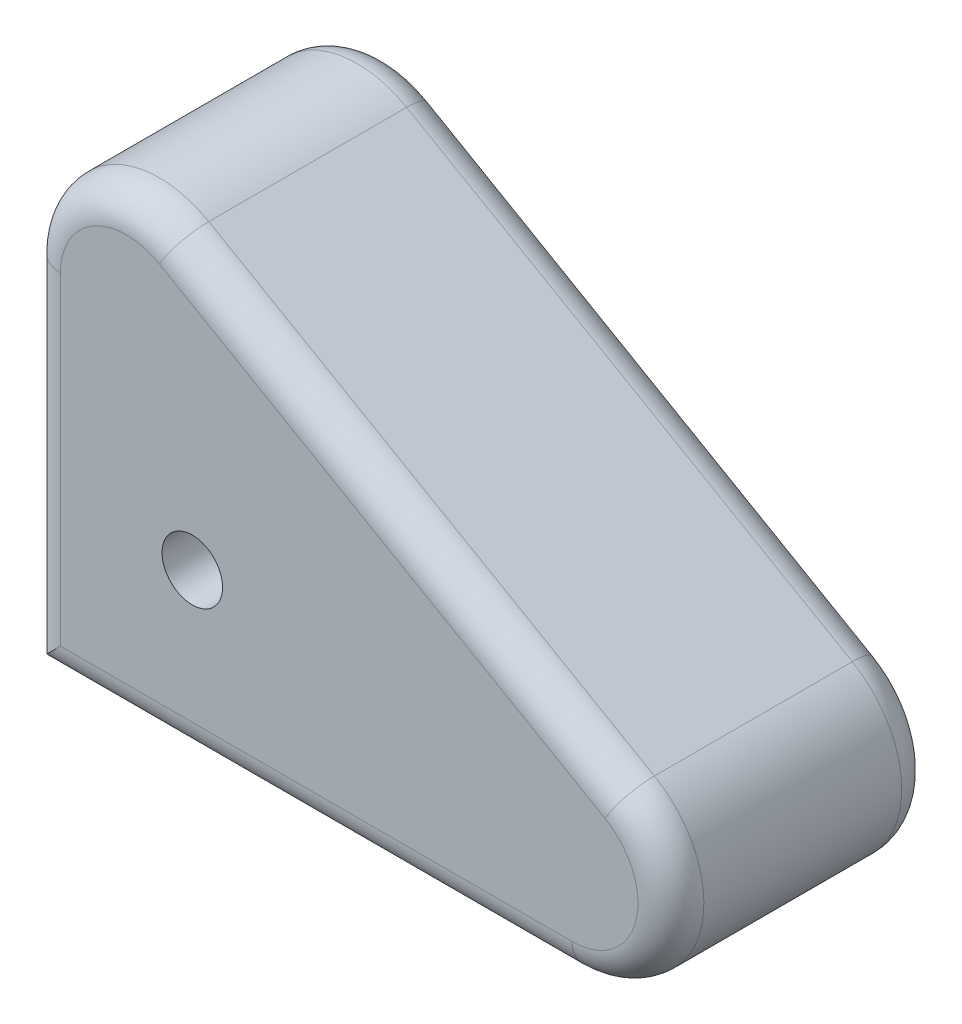
SolidWorks part; units mm, degrees
material "Custom Plastic"
ref_plane "Front Plane" through (0, 0, 0) normal (0, 0, 1) x (1, 0, 0)
ref_plane "Top Plane" through (0, 0, 0) normal (0, 1, 0) x (1, 0, 0)
ref_plane "Right Plane" through (0, 0, 0) normal (1, 0, 0) x (0, 0, -1)
sketch "Sketch1" plane through (0, 0, 0) normal (0, 0, 1) x (1, 0, 0)
  line L0 (-31.75, -31.75) -> (73.1308, -31.75)
  line L1 (82.6558, 3.7978) -> (-3.175, 53.3522)
  line L2 (-31.75, 36.8544) -> (-31.75, -31.75)
  circle A0 centre (0, 0) radius 5.8301
  arc A1 (82.6558, 3.7978) -> (73.1308, -31.75) centre (73.1308, -12.7) cw
  arc A2 (-3.175, 53.3522) -> (-31.75, 36.8544) centre (-12.7, 36.8544) ccw
  point P12 (-31.75, 69.85)
  dimension "D4" = 11.6602
  dimension "D6" = 19.05
  dimension "D1" = 31.75
  dimension "D2" = 31.75
  dimension "D3" = 101.6
  dimension "D5" = 30
extrude "Boss-Extrude1" add sketch "Sketch1" along normal blind 50.8
fillet "Fillet1" radius 6.35 10 edges at (20.6904, -31.75, 0) (91.5317, -17.6305, 0) (-31.75, 2.5522, 0) (-22.225, 53.3522, 0) (20.6904, -31.75, 50.8) (91.5317, -17.6305, 50.8) (-31.75, 2.5522, 50.8) (-22.225, 53.3522, 50.8) (39.7404, 28.575, 0) (39.7404, 28.575, 50.8)
